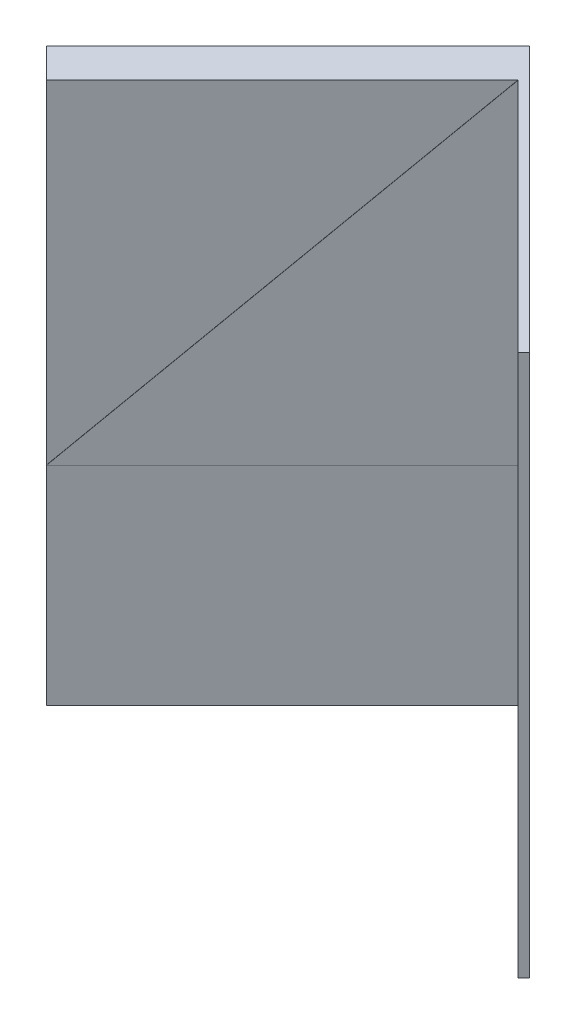
SolidWorks part; units mm, degrees
material "Nickel"
ref_plane "Front Plane" through (0, 0, 0) normal (0, 0, 1) x (1, 0, 0)
ref_plane "Top Plane" through (0, 0, 0) normal (0, 1, 0) x (1, 0, 0)
ref_plane "Right Plane" through (0, 0, 0) normal (1, 0, 0) x (0, 0, -1)
sketch "Sketch1" plane through (0, 0, 0) normal (0, 1, 0) x (1, 0, 0)
  line L0 (0, 0) -> (-143.6841, -143.6841)
  line L1 (-143.6841, -143.6841) -> (-161.6446, -125.7236)
  line L2 (-161.6446, -125.7236) -> (-14.3684, 21.5526)
  line L4 (-14.3684, 21.5526) -> (147.2762, -140.092)
  line L5 (147.2762, -140.092) -> (143.6841, -143.6841)
  line L6 (143.6841, -143.6841) -> (0, 0)
  line L7 (0, 0) -> (0, -79.2671) construction
  dimension "D1" = 5.08
  dimension "D2" = 25.4
  dimension "D3" = 203.2
  dimension "D4" = 45
extrude "Boss-Extrude1" add sketch "Sketch1" along normal blind 330.2
sketch "Sketch2" plane through (0, 0, 0) normal (0.7071, 0, 0.7071) x (0.7071, 0, -0.7071)
  line L0 (0, 330.2) -> (0, 127)
  line L1 (0, 330.2) -> (0, 0) construction
  line L4 (0, 127) -> (-203.2, 127)
  line L5 (-203.2, 330.2) -> (-203.2, 0) construction
  line L6 (-203.2, 127) -> (0, 330.2)
  dimension "D1" = 45
extrude "Boss-Extrude2" add sketch "Sketch2" along normal blind 0.254
